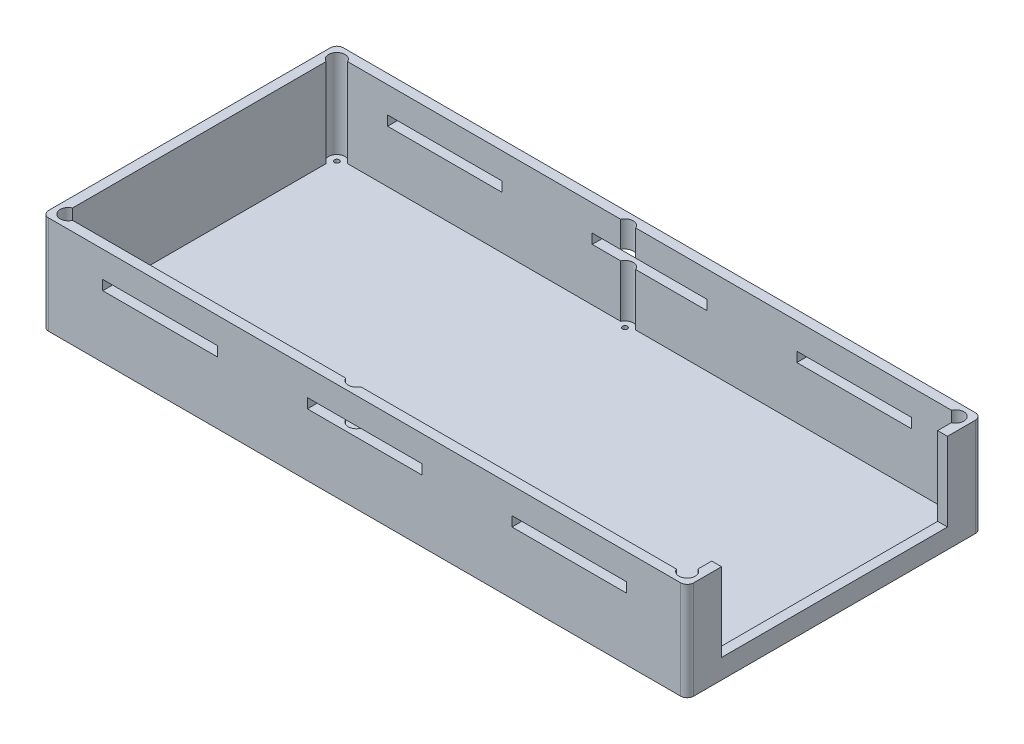
SolidWorks part; units mm, degrees
ref_plane "Front Plane" through (0, 0, 0) normal (0, 0, 1) x (1, 0, 0)
ref_plane "Top Plane" through (0, 0, 0) normal (0, 1, 0) x (1, 0, 0)
ref_plane "Right Plane" through (0, 0, 0) normal (1, 0, 0) x (0, 0, -1)
sketch "Sketch2" plane through (0, 0, 0) normal (0, 1, 0) x (1, 0, 0)
  line L1 (0, 0) -> (197, 0)
  line L2 (0, 0) -> (0, 90)
  line L3 (0, 90) -> (197, 90)
  line L4 (197, 0) -> (197, 90)
  dimension "D1" = 197
  dimension "D2" = 90
extrude "Boss-Extrude1" add sketch "Sketch2" along normal blind 21
shell "Shell1" thickness 2
sketch "Sketch3" plane through (0.4867, 2, 38.6702) normal (0, 1, 0) x (1, 0, 0)
  circle A0 centre (118.949, 112.1395) radius 1.325
  circle A1 centre (118.949, 54.0895) radius 3.325
  circle A2 centre (95.899, 54.0895) radius 3.325
  circle A3 centre (95.899, 112.1395) radius 3.325
  circle A4 centre (118.949, 112.1395) radius 3.325
  circle A5 centre (95.899, 112.1395) radius 1.325
  circle A6 centre (95.899, 54.0895) radius 1.325
  circle A7 centre (118.949, 54.0895) radius 1.325
extrude "Boss-Extrude2" add sketch "Sketch3" along normal blind 2
sketch "Sketch6" plane through (0, 2, 0) normal (0, 1, 0) x (1, 0, 0)
  circle A0 centre (119.4356, 73.4693) radius 1.325 construction
  circle A1 centre (96.3856, 73.4693) radius 1.325
  circle A2 centre (96.3856, 73.4693) radius 1.325
  circle A3 centre (119.4356, 15.4193) radius 1.325 construction
  circle A4 centre (96.3856, 15.4193) radius 1.325 construction
  circle A5 centre (119.4356, 73.4693) radius 1.325
  circle A6 centre (119.4356, 15.4193) radius 1.325
  circle A7 centre (96.3856, 15.4193) radius 1.325
  dimension "D1" = 0
extrude "Cut-Extrude2" cut sketch "Sketch6" against normal through all
sketch "Sketch7" plane through (0, 0, 0) normal (-1, 0, 0) x (0, 0, 1)
  line L1 (-90, 10.5) -> (-83.6201, 10.5) construction
  line L2 (-90, 21) -> (-90, 0) construction
  circle A0 centre (-57.5, 13.5) radius 6
  dimension "D1" = 12
  dimension "D2" = 3
  dimension "D3" = 32.5
sketch "Sketch8" plane through (0, 2, 0) normal (0, 1, 0) x (1, 0, 0)
  line L0 (2, 88) -> (2, 2) construction
  line L1 (2, 28) -> (87, 28)
  line L2 (2, 45) -> (15.4419, 45) construction
  line L3 (2, 87) -> (87, 87)
  line L4 (87, 28) -> (87, 87)
  line L5 (2, 88) -> (2, 2) construction
  line L7 (2, 25) -> (90, 25)
  line L8 (90, 25) -> (90, 90)
  line L9 (2, 90) -> (90, 90)
  line L10 (2, 25) -> (2, 28)
  line L11 (2, 87) -> (2, 90)
  line L12 (197, 90) -> (0, 90) construction
  dimension "D1" = 59
  dimension "D2" = 0
  dimension "D3" = 85
  dimension "D4" = 3
extrude "Boss-Extrude3" add sketch "Sketch8" along normal up to surface (19 mm away) up to face at (98.5, 21, -45)
sketch "Sketch10" plane through (0, 21, 0) normal (0, 1, 0) x (1, 0, 0)
  line L0 (87, 57.5) -> (90, 57.5) construction
  line L2 (90, 25) -> (90, 88) construction
  line L3 (87, 87) -> (87, 28) construction
  line L4 (87, 51.5) -> (90, 51.5)
  line L5 (87, 51.5) -> (87, 63.5)
  line L6 (87, 63.5) -> (90, 63.5)
  line L7 (90, 51.5) -> (90, 63.5)
  line L8 (87, 28) -> (87, 87) construction
  line L9 (90, 25) -> (90, 88) construction
  dimension "D1" = 12
  dimension "D2" = 6
extrude "Cut-Extrude5" cut sketch "Sketch10" against normal up to surface (19 mm away) up to face at (119.4356, 2, -18.7443)
sketch "Sketch12" plane through (0, 0, -75) normal (0, 0, -1) x (-1, 0, 0)
  line L1 (-57.7754, 12.1097) -> (-28.1833, 12.1097)
  line L2 (-57.7754, 12.1097) -> (-57.7754, 14.1097)
  line L3 (-57.7754, 14.1097) -> (-28.1833, 14.1097)
  line L4 (-28.1833, 12.1097) -> (-28.1833, 14.1097)
  line L5 (-57.7754, 7.1097) -> (-28.1833, 7.1097)
  line L6 (-57.7754, 7.1097) -> (-57.7754, 9.1097)
  line L7 (-57.7754, 9.1097) -> (-28.1833, 9.1097)
  line L8 (-28.1833, 7.1097) -> (-28.1833, 9.1097)
  dimension "D1" = 2
  dimension "D2" = 2
  dimension "D3" = 3
extrude "Cut-Extrude6" cut sketch "Sketch12" against normal up to surface (73 mm away) and the other way blind 10 up to face at (98.5, 11.5, -2)
sketch "Sketch16" plane through (197, 0, 0) normal (1, 0, 0) x (0, 0, -1)
  line L0 (45, 21) -> (45, 0) construction
  line L1 (0, 21) -> (90, 21) construction
  line L2 (0, 0) -> (90, 0) construction
  line L3 (48, 14.2355) -> (48, 21)
  line L4 (48, 21) -> (42, 21)
  line L5 (42, 21) -> (42, 14.2355)
  arc A0 (42, 14.2355) -> (48, 14.2355) centre (45, 14.2355) ccw
  dimension "D1" = 6
extrude "Cut-Extrude8" cut sketch "Sketch16" against normal blind 10
fillet "Fillet1" radius 2 8 edges at (0, 10.5, -90) (197, 10.5, -90) (197, 10.5, 0) (197, 0, -45) (98.5, 0, -90) (0, 0, -45) (98.5, 0, 0) (0, 10.5, 0)
extrude "Cut-Extrude9" cut sketch "Sketch7" against normal blind 10
sketch "Sketch17" plane through (0, 21, 0) normal (0, 1, 0) x (1, 0, 0)
  line L0 (197, 48) -> (197, 42)
  line L22 (195, 90) -> (2, 90)
  line L23 (0, 88) -> (0, 2)
  line L24 (2, 0) -> (195, 0)
  line L25 (197, 2) -> (197, 42)
  line L27 (197, 42) -> (195, 42)
  line L28 (195, 42) -> (195, 2)
  line L29 (195, 2) -> (2, 2)
  line L30 (2, 2) -> (2, 25)
  line L31 (2, 25) -> (90, 25)
  line L32 (90, 25) -> (90, 51.5)
  line L33 (90, 51.5) -> (87, 51.5)
  line L34 (87, 51.5) -> (87, 28)
  line L35 (87, 28) -> (2, 28)
  line L36 (2, 28) -> (2, 87)
  line L37 (2, 87) -> (87, 87)
  line L38 (87, 87) -> (87, 63.5)
  line L39 (87, 63.5) -> (90, 63.5)
  line L40 (90, 63.5) -> (90, 88)
  line L41 (90, 88) -> (195, 88)
  line L42 (195, 88) -> (195, 48)
  line L43 (195, 48) -> (197, 48)
  line L44 (195, 90) -> (2, 90)
  line L45 (0, 88) -> (0, 2)
  line L46 (2, 0) -> (195, 0)
  line L47 (197, 2) -> (197, 42)
  line L48 (197, 48) -> (197, 88)
  line L49 (197, 48) -> (197, 88)
  arc A4 (2, 90) -> (0, 88) centre (2, 88) ccw
  arc A5 (0, 2) -> (2, 0) centre (2, 2) ccw
  arc A6 (195, 0) -> (197, 2) centre (195, 2) ccw
  arc A7 (197, 88) -> (195, 90) centre (195, 88) ccw
  arc A8 (2, 90) -> (0, 88) centre (2, 88) ccw
  arc A9 (0, 2) -> (2, 0) centre (2, 2) ccw
  arc A10 (195, 0) -> (197, 2) centre (195, 2) ccw
  arc A11 (197, 88) -> (195, 90) centre (195, 88) ccw
  dimension "D1" = 0
extrude "Boss-Extrude4" add sketch "Sketch17" along normal blind 24
sketch "Sketch18" plane through (0, 45, 0) normal (0, 1, 0) x (1, 0, 0)
  line L8 (194, 87) -> (3, 87)
  line L9 (3, 87) -> (3, 3)
  line L10 (3, 3) -> (194, 3)
  line L11 (194, 3) -> (194, 87)
  line L12 (194, 87) -> (3, 87)
  line L13 (3, 87) -> (3, 3)
  line L14 (3, 3) -> (194, 3)
  line L15 (194, 3) -> (194, 87)
  dimension "D1" = 3
extrude "Cut-Extrude10" cut sketch "Sketch18" against normal offset from surface (21 mm away) 3 up to face at (105, 21, -48.3333)
sketch "Sketch19" plane through (0, 2, 0) normal (0, 1, 0) x (1, 0, 0)
  line L0 (193, 88) -> (195, 88)
  line L1 (195, 88) -> (195, 84)
  line L2 (191, 86) -> (191, 88)
  line L3 (2, 2) -> (195, 2) construction
  line L4 (2, 25) -> (2, 2) construction
  line L5 (2, 2) -> (2, 88) construction
  line L6 (195, 90) -> (2, 90) construction
  line L7 (195, 2) -> (195, 88) construction
  line L8 (90, 63.5) -> (90, 88) construction
  line L9 (193, 84) -> (195, 84)
  line L10 (195, 88) -> (90, 88) construction
  line L11 (194, 45) -> (197, 45) construction
  line L12 (194, 3) -> (194, 87) construction
  line L13 (197, 2) -> (197, 88) construction
  line L14 (191, 2) -> (193, 2)
  line L15 (94, 4) -> (94, 2)
  line L16 (90, 4) -> (90, 2)
  line L17 (92, 84) -> (90, 84)
  line L18 (94, 86) -> (94, 88)
  line L19 (2, 88) -> (2, 84)
  line L20 (2, 88) -> (195, 88) construction
  line L21 (94, 88) -> (90, 88)
  line L22 (90, 84) -> (90, 88)
  line L23 (6, 4) -> (6, 2)
  line L24 (6, 2) -> (2, 2)
  line L25 (2, 2) -> (2, 6)
  line L26 (2, 6) -> (4, 6)
  line L27 (193, 6) -> (195, 6)
  line L28 (2, 84) -> (4, 84)
  line L29 (2, 88) -> (6, 88)
  line L30 (6, 88) -> (6, 86)
  line L31 (191, 88) -> (193, 88)
  line L32 (90, 2) -> (94, 2)
  line L33 (191, 4) -> (191, 2)
  line L34 (195, 2) -> (195, 6)
  line L35 (193, 2) -> (195, 2)
  arc A0 (6, 4) -> (4, 6) centre (4, 4) ccw
  arc A1 (4, 84) -> (6, 86) centre (4, 86) ccw
  arc A2 (191, 86) -> (193, 84) centre (193, 86) ccw
  arc A3 (191, 4) -> (193, 6) centre (193, 4) cw
  arc A4 (92, 84) -> (94, 86) centre (92, 86) ccw
  arc A5 (94, 4) -> (90, 4) centre (92, 4) ccw
  dimension "D1" = 2
  dimension "D2" = 2
  dimension "D3" = 4
  dimension "D6" = 4
  dimension "D7" = 4
  dimension "D9" = 4
  dimension "D4" = 2
  dimension "D5" = 4
  dimension "D8" = 2
  dimension "D10" = 2
extrude "Boss-Extrude5" add sketch "Sketch19" along direction (0, 1, 0) on the side of the normal up to surface (19 mm away)
sketch "Sketch22" plane through (0, 2, 0) normal (0, 1, 0) x (1, 0, 0)
  circle A0 centre (4, 4) radius 0.75
  circle A1 centre (4, 86) radius 0.75
  circle A2 centre (92, 86) radius 0.75
  circle A3 centre (193, 86) radius 0.75
  circle A4 centre (193, 4) radius 0.75
  circle A5 centre (92, 4) radius 0.75
  dimension "D1" = 1.5
  dimension "D2" = 1.5
  dimension "D3" = 1.5
  dimension "D4" = 1.5
  dimension "D5" = 1.5
  dimension "D6" = 1.5
extrude "Cut-Extrude11" cut sketch "Sketch22" along normal through all
sketch "Sketch23" plane through (0, 24, 0) normal (0, 1, 0) x (1, 0, 0)
  circle A0 centre (92, 4) radius 2
  circle A1 centre (4, 4) radius 2
  circle A2 centre (4, 86) radius 2
  circle A3 centre (92, 86) radius 2
  circle A4 centre (193, 86) radius 2
  circle A5 centre (181, 4) radius 2
  dimension "D1" = 4
  dimension "D2" = 4
  dimension "D3" = 4
  dimension "D4" = 4
  dimension "D5" = 4
  dimension "D6" = 4
extrude "Cut-Extrude12" cut sketch "Sketch23" along normal through all
sketch "Sketch24" plane through (0, 0, 0) normal (0, 0, 1) x (1, 0, 0)
  line L0 (197, 45) -> (197, 2) construction
  line L1 (0, 45) -> (197, 45)
  line L2 (0, 45) -> (0, 21)
  line L3 (0, 21) -> (197, 21)
  line L4 (197, 45) -> (197, 21)
  dimension "D1" = 24
extrude "Cut-Extrude13" cut sketch "Sketch24" against normal through all
sketch "Sketch25" plane through (0, 21, 0) normal (0, 1, 0) x (1, 0, 0)
  line L0 (2, 25) -> (2, 28)
  line L1 (90, 84) -> (90, 87)
  line L2 (90, 87) -> (87, 87)
  line L3 (195, 42) -> (195, 48)
  line L4 (197, 42) -> (197, 48)
  line L35 (197, 2) -> (197, 42)
  line L36 (197, 42) -> (195, 42)
  line L37 (195, 42) -> (195, 6)
  line L38 (195, 6) -> (193, 6)
  line L39 (191, 4) -> (191, 2)
  line L40 (191, 2) -> (94, 2)
  line L41 (94, 2) -> (94, 4)
  line L42 (90, 4) -> (90, 2)
  line L43 (90, 2) -> (6, 2)
  line L44 (6, 2) -> (6, 4)
  line L45 (4, 6) -> (2, 6)
  line L46 (2, 6) -> (2, 25)
  line L47 (2, 25) -> (90, 25)
  line L48 (90, 25) -> (90, 51.5)
  line L49 (90, 51.5) -> (87, 51.5)
  line L50 (87, 51.5) -> (87, 28)
  line L51 (87, 28) -> (2, 28)
  line L52 (2, 28) -> (2, 84)
  line L53 (2, 84) -> (4, 84)
  line L54 (6, 86) -> (6, 87)
  line L55 (6, 87) -> (87, 87)
  line L56 (87, 87) -> (87, 63.5)
  line L57 (87, 63.5) -> (90, 63.5)
  line L58 (90, 63.5) -> (90, 84)
  line L59 (90, 84) -> (92, 84)
  line L60 (94, 86) -> (94, 88)
  line L61 (94, 88) -> (191, 88)
  line L62 (191, 88) -> (191, 86)
  line L63 (193, 84) -> (195, 84)
  line L64 (195, 84) -> (195, 48)
  line L65 (195, 48) -> (197, 48)
  line L66 (197, 48) -> (197, 88)
  line L67 (195, 90) -> (2, 90)
  line L68 (0, 88) -> (0, 2)
  line L69 (2, 0) -> (195, 0)
  line L70 (197, 2) -> (197, 42)
  line L72 (195, 42) -> (195, 6)
  line L73 (195, 6) -> (193, 6)
  line L74 (191, 4) -> (191, 2)
  line L75 (191, 2) -> (94, 2)
  line L76 (94, 2) -> (94, 4)
  line L77 (90, 4) -> (90, 2)
  line L78 (90, 2) -> (6, 2)
  line L79 (6, 2) -> (6, 4)
  line L80 (4, 6) -> (2, 6)
  line L81 (2, 6) -> (2, 25)
  line L87 (2, 28) -> (2, 84)
  line L88 (2, 84) -> (4, 84)
  line L89 (6, 86) -> (6, 87)
  line L90 (6, 87) -> (87, 87)
  line L94 (90, 84) -> (92, 84)
  line L95 (94, 86) -> (94, 88)
  line L96 (94, 88) -> (191, 88)
  line L97 (191, 88) -> (191, 86)
  line L98 (193, 84) -> (195, 84)
  line L99 (195, 84) -> (195, 48)
  line L101 (197, 48) -> (197, 88)
  line L102 (195, 90) -> (2, 90)
  line L103 (0, 88) -> (0, 2)
  line L104 (2, 0) -> (195, 0)
  circle A0 centre (4, 4) radius 0.75 construction
  circle A1 centre (4, 86) radius 0.75 construction
  circle A2 centre (92, 86) radius 0.75 construction
  circle A3 centre (193, 86) radius 0.75 construction
  circle A4 centre (193, 4) radius 0.75 construction
  circle A5 centre (92, 4) radius 0.75 construction
  circle A6 centre (4, 4) radius 0.75
  circle A7 centre (4, 86) radius 0.75
  circle A8 centre (92, 86) radius 0.75
  circle A9 centre (193, 86) radius 0.75
  arc A10 (195, 0) -> (197, 2) centre (195, 2) ccw
  arc A11 (193, 6) -> (191, 4) centre (193, 4) ccw
  arc A12 (94, 4) -> (90, 4) centre (92, 4) ccw
  arc A13 (6, 4) -> (4, 6) centre (4, 4) ccw
  arc A14 (4, 84) -> (6, 86) centre (4, 86) ccw
  arc A15 (92, 84) -> (94, 86) centre (92, 86) ccw
  arc A16 (191, 86) -> (193, 84) centre (193, 86) ccw
  arc A17 (197, 88) -> (195, 90) centre (195, 88) ccw
  arc A18 (2, 90) -> (0, 88) centre (2, 88) ccw
  arc A19 (0, 2) -> (2, 0) centre (2, 2) ccw
  arc A20 (195, 0) -> (197, 2) centre (195, 2) ccw
  arc A21 (193, 6) -> (191, 4) centre (193, 4) ccw
  arc A22 (94, 4) -> (90, 4) centre (92, 4) ccw
  arc A23 (6, 4) -> (4, 6) centre (4, 4) ccw
  arc A24 (4, 84) -> (6, 86) centre (4, 86) ccw
  arc A25 (92, 84) -> (94, 86) centre (92, 86) ccw
  arc A26 (191, 86) -> (193, 84) centre (193, 86) ccw
  arc A27 (197, 88) -> (195, 90) centre (195, 88) ccw
  arc A28 (2, 90) -> (0, 88) centre (2, 88) ccw
  arc A29 (0, 2) -> (2, 0) centre (2, 2) ccw
  circle A30 centre (193, 4) radius 0.75
  circle A31 centre (92, 4) radius 0.75
  dimension "D1" = 0
extrude "Boss-Extrude9" add sketch "Sketch25" along normal blind 28
sketch "Sketch26" plane through (197, 0, 0) normal (1, 0, 0) x (0, 0, -1)
  line L0 (48, 21) -> (42, 21)
  line L1 (42, 21) -> (42, 14.2355)
  line L2 (48, 14.2355) -> (48, 21)
  arc A0 (42, 14.2355) -> (48, 14.2355) centre (45, 14.2355) ccw
extrude "Boss-Extrude10" add sketch "Sketch26" against normal up to surface (2 mm away)
sketch "Sketch27" plane through (0, 49, 0) normal (0, 1, 0) x (1, 0, 0)
  line L0 (197, 2) -> (197, 88) construction
  line L1 (195, 90) -> (2, 90) construction
  line L2 (2, 0) -> (195, 0) construction
  line L3 (0, 88) -> (0, 2) construction
  line L4 (197, 2) -> (197, 88)
  line L5 (195, 90) -> (2, 90)
  line L6 (2, 0) -> (195, 0)
  line L7 (0, 88) -> (0, 2)
  arc A0 (195, 0) -> (197, 2) centre (195, 2) ccw construction
  arc A1 (197, 88) -> (195, 90) centre (195, 88) ccw construction
  arc A2 (2, 90) -> (0, 88) centre (2, 88) ccw construction
  arc A3 (0, 2) -> (2, 0) centre (2, 2) ccw construction
  arc A4 (195, 0) -> (197, 2) centre (195, 2) ccw
  arc A5 (197, 88) -> (195, 90) centre (195, 88) ccw
  arc A6 (2, 90) -> (0, 88) centre (2, 88) ccw
  arc A7 (0, 2) -> (2, 0) centre (2, 2) ccw
extrude "Boss-Extrude11" add sketch "Sketch27" along normal blind 30
sketch "Sketch28" plane through (0, 79, 0) normal (0, 1, 0) x (1, 0, 0)
  line L8 (194, 3) -> (194, 87)
  line L9 (194, 87) -> (3, 87)
  line L10 (3, 87) -> (3, 3)
  line L11 (3, 3) -> (194, 3)
  line L12 (194, 3) -> (194, 87)
  line L13 (194, 87) -> (3, 87)
  line L14 (3, 87) -> (3, 3)
  line L15 (3, 3) -> (194, 3)
  dimension "D1" = 3
extrude "Cut-Extrude14" cut sketch "Sketch28" against normal blind 27
sketch "Sketch29" plane through (0, 2, 0) normal (0, 1, 0) x (1, 0, 0)
  circle A0 centre (4, 4) radius 0.75 construction
  circle A1 centre (4, 86) radius 0.75 construction
  circle A2 centre (193, 86) radius 0.75 construction
  circle A3 centre (193, 4) radius 0.75 construction
  circle A4 centre (92, 4) radius 0.75 construction
  circle A5 centre (92, 86) radius 0.75 construction
  circle A6 centre (4, 4) radius 0.75
  circle A7 centre (4, 86) radius 0.75
  circle A8 centre (193, 86) radius 0.75
  circle A9 centre (193, 4) radius 0.75
  circle A10 centre (92, 4) radius 0.75
  circle A11 centre (92, 86) radius 0.75
extrude "Cut-Extrude15" cut sketch "Sketch29" along normal through all
sketch "Sketch30" plane through (0, 0, 0) normal (0, 0, 1) x (1, 0, 0)
  line L0 (197, 79) -> (197, 2) construction
  line L1 (0, 0) -> (197, 0)
  line L2 (0, 0) -> (0, 49)
  line L3 (0, 49) -> (197, 49)
  line L4 (197, 0) -> (197, 49)
  line L5 (2, 79) -> (195, 79) construction
  dimension "D1" = 30
extrude "Cut-Extrude16" cut sketch "Sketch30" against normal through all
sketch "Sketch31" plane through (197, 0, 0) normal (1, 0, 0) x (0, 0, -1)
  line L0 (2, 79) -> (88, 79) construction
  line L1 (10.5, 79) -> (79.5, 79)
  line L2 (10.5, 79) -> (10.5, 55)
  line L3 (10.5, 55) -> (79.5, 55)
  line L4 (79.5, 79) -> (79.5, 55)
  line L5 (0, 49) -> (0, 79) construction
  line L6 (90, 79) -> (90, 49) construction
  line L7 (88, 49) -> (2, 49) construction
  point P10 (90, 64)
  dimension "D1" = 10.5
  dimension "D2" = 10.5
  dimension "D3" = 6
extrude "Cut-Extrude17" cut sketch "Sketch31" against normal blind 10
sketch "Sketch32" plane through (0, 52, 0) normal (0, 1, 0) x (1, 0, 0)
  circle A0 centre (4, 4) radius 2.5
  circle A1 centre (4, 86) radius 2.5
  circle A2 centre (92, 86) radius 2.5
  circle A3 centre (193, 86) radius 2.5
  circle A4 centre (193, 4) radius 2.5
  circle A5 centre (92, 4) radius 2.5
  dimension "D1" = 5
  dimension "D2" = 5
  dimension "D3" = 5
  dimension "D4" = 5
  dimension "D5" = 5
  dimension "D6" = 5
extrude "Cut-Extrude18" cut sketch "Sketch32" along normal through all
sketch "Sketch33" plane through (0, 0, 0) normal (0, 0, 1) x (1, 0, 0)
  line L0 (98.5, 79) -> (98.5, 49) construction
  line L1 (2, 79) -> (195, 79) construction
  line L2 (195, 49) -> (2, 49) construction
  line L4 (18.5, 71) -> (53.5, 71)
  line L5 (18.5, 71) -> (18.5, 68)
  line L6 (18.5, 68) -> (53.5, 68)
  line L7 (53.5, 71) -> (53.5, 68)
  line L8 (81, 71) -> (116, 71)
  line L9 (81, 71) -> (81, 68)
  line L10 (81, 68) -> (116, 68)
  line L11 (116, 71) -> (116, 68)
  line L12 (143.5, 71) -> (178.5, 71)
  line L13 (143.5, 71) -> (143.5, 68)
  line L14 (143.5, 68) -> (178.5, 68)
  line L15 (178.5, 71) -> (178.5, 68)
  dimension "D1" = 35
  dimension "D2" = 35
  dimension "D3" = 35
  dimension "D4" = 17.5
  dimension "D5" = 45
  dimension "D6" = 27.5
  dimension "D7" = 8
  dimension "D8" = 8
  dimension "D9" = 8
  dimension "D10" = 3
  dimension "D11" = 3
  dimension "D12" = 3
extrude "Cut-Extrude19" cut sketch "Sketch33" against normal through all
